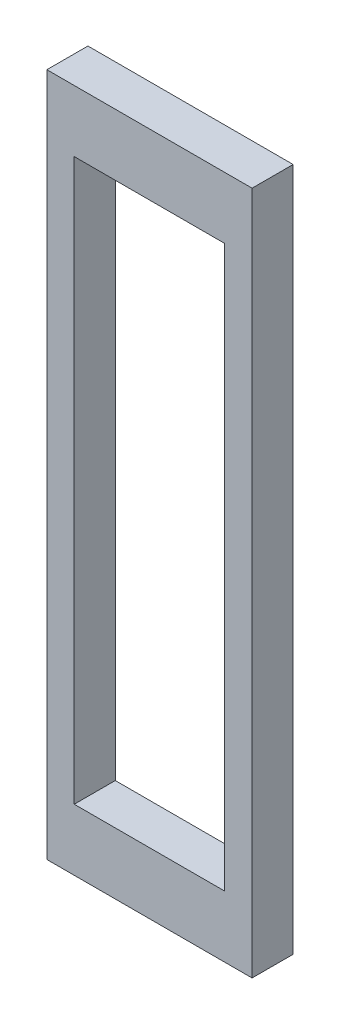
SolidWorks part; units mm, degrees
material "고무"
ref_plane "정면" through (0, 0, 0) normal (0, 0, 1) x (1, 0, 0)
ref_plane "윗면" through (0, 0, 0) normal (0, 1, 0) x (1, 0, 0)
ref_plane "우측면" through (0, 0, 0) normal (1, 0, 0) x (0, 0, -1)
sketch "스케치3" plane through (0, 0, 0) normal (0, 0, -1) x (-1, 0, 0)
  line L0 (0, 0) -> (0, 9.7101) construction
  line L1 (-7.5, 25) -> (7.5, 25)
  line L2 (-7.5, 25) -> (-7.5, -25)
  line L3 (-7.5, -25) -> (7.5, -25)
  line L4 (7.5, 25) -> (7.5, -25)
  line L5 (-7.5, 25) -> (7.5, -25) construction
  line L6 (-7.5, -25) -> (7.5, 25) construction
  line L7 (-5.5, 20.5) -> (5.5, 20.5)
  line L8 (-5.5, 20.5) -> (-5.5, -20.5)
  line L9 (-5.5, -20.5) -> (5.5, -20.5)
  line L18 (5.5, 20.5) -> (5.5, -20.5)
  line L21 (0, 0) -> (18.5385, 0) construction
  point P0 (0, 0)
  point P7 (0, 0)
  dimension "D1" = 41
  dimension "D2" = 11
  dimension "D4" = 50
  dimension "D5" = 15
extrude "보스-돌출1" add sketch "스케치3" along normal blind 3
